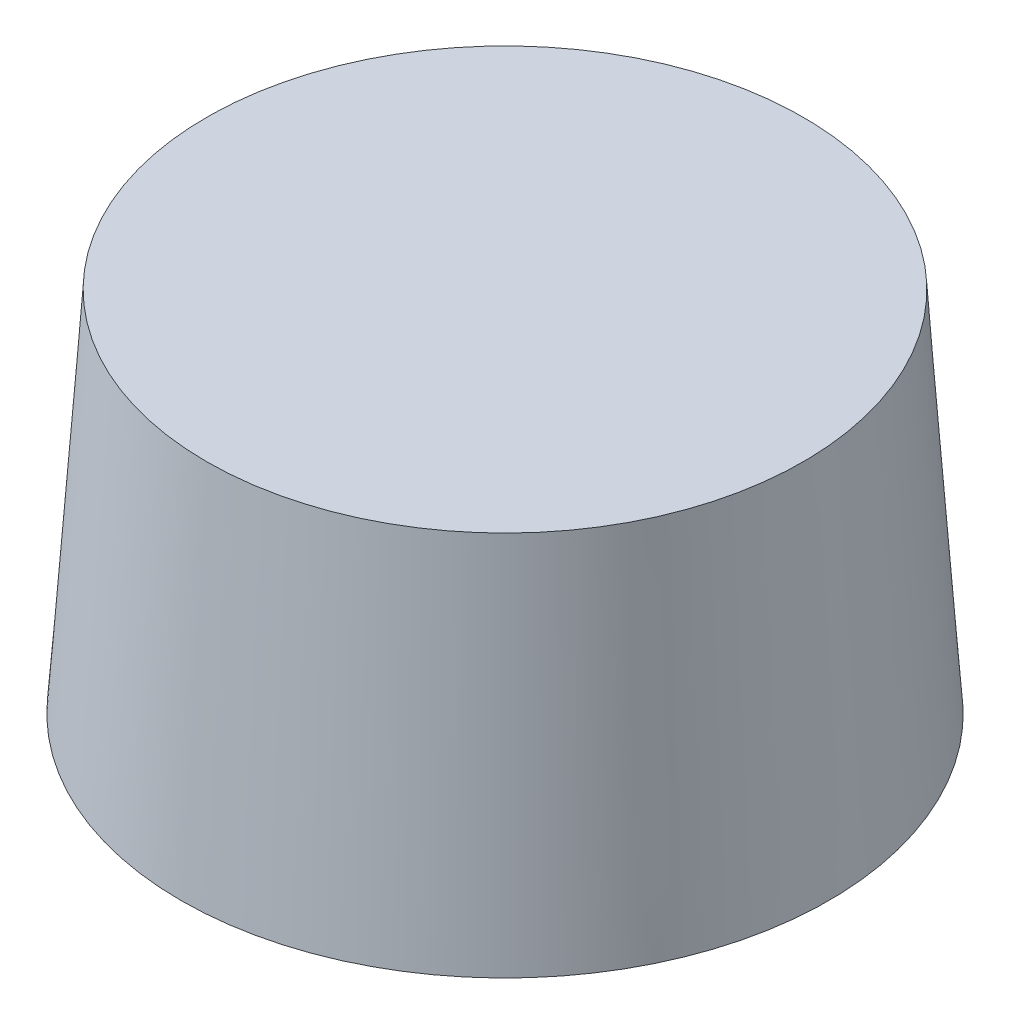
SolidWorks part; units mm, degrees
ref_plane "前视基准面" through (0, 0, 0) normal (0, 0, 1) x (1, 0, 0)
ref_plane "上视基准面" through (0, 0, 0) normal (0, 1, 0) x (1, 0, 0)
ref_plane "右视基准面" through (0, 0, 0) normal (1, 0, 0) x (0, 0, -1)
sketch "草图1" plane through (0, 0, 0) normal (0, 1, 0) x (1, 0, 0)
  circle A0 centre (0, 0) radius 32.5
  dimension "D1" = 65
extrude "凸台-拉伸1" add sketch "草图1" along normal blind 40
draft "拔模1" type of draft neutral plane draft angle 4 faces to draft 1 face at (0, 40, 32.5) neutral plane through (0, 40, 0) neutral plane normal (0, 1, 0) parameters "D1"=4
